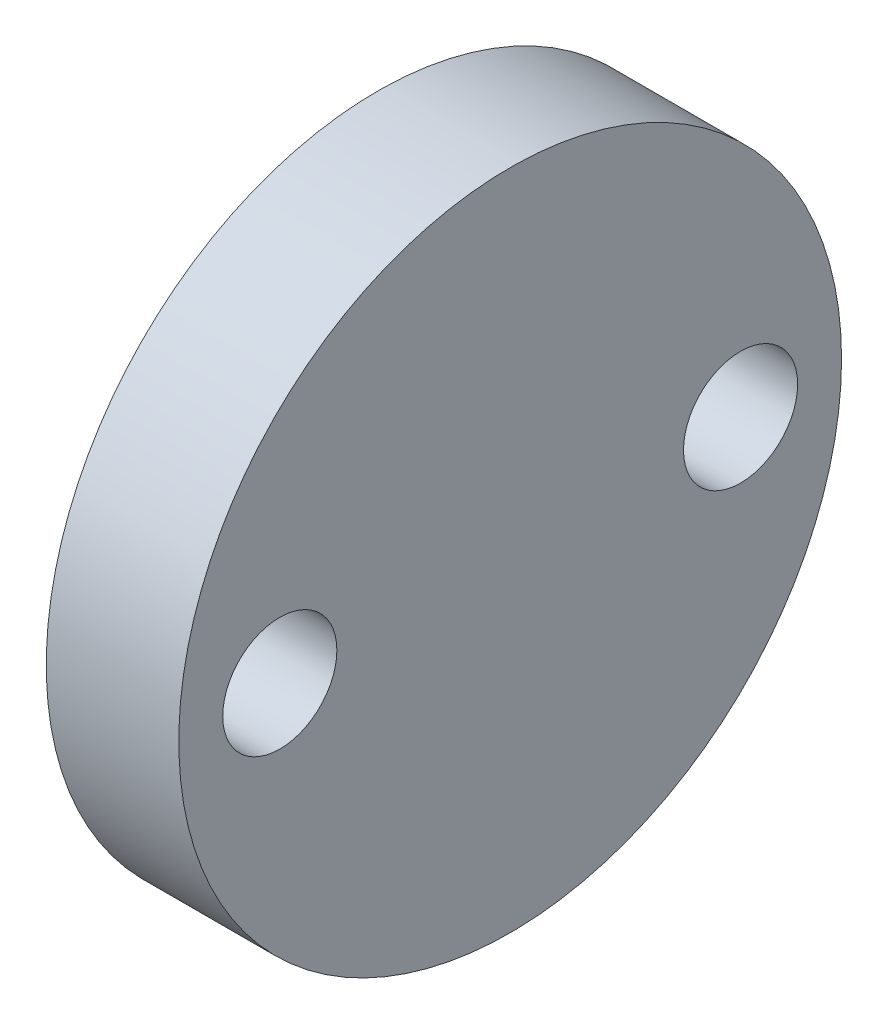
SolidWorks part; units mm, degrees
ref_plane "Front Plane" through (0, 0, 0) normal (0, 0, 1) x (1, 0, 0)
ref_plane "Top Plane" through (0, 0, 0) normal (0, 1, 0) x (1, 0, 0)
ref_plane "Right Plane" through (0, 0, 0) normal (1, 0, 0) x (0, 0, -1)
sketch "Sketch1" plane through (0, 0, 0) normal (1, 0, 0) x (0, 0, -1)
  line L0 (-12.5, 0) -> (12.5, 0) construction
  circle A0 centre (0, 0) radius 12.5
  dimension "D1" = 25
extrude "Boss-Extrude1" add sketch "Sketch1" along normal blind 5
hole_wizard "#18 (0.1695) Diameter Hole2" positions "Sketch5" profile "Sketch6" hole size "#18" standard "ANSI Inch"
sketch "Sketch5" plane through (0, 0, 0) normal (-1, 0, 0) x (0, 0, 1)
  line L0 (-12.5, 0) -> (12.5, 0) construction
  circle A0 centre (0, 0) radius 12.5 construction
  point P0 (-8.69, 0)
  point P2 (8.69, 0)
  dimension "D1" = 3.81
  dimension "D2" = 3.81
sketch "Sketch6" plane through (0, 0, -8.69) normal (0, 1, 0) x (0, 0, 1)
  line L0 (0, 0) -> (0, 11.4026)
  line L1 (0, 11.4026) -> (2.1526, 10.1092)
  line L2 (2.1526, 10.1092) -> (2.1526, 0)
  line L5 (2.1526, 0) -> (0, 0)
  line L10 (0, 11.4026) -> (-2.1526, 10.1092) construction
  line L11 (0, -6.35) -> (0, 107.95) construction
  dimension "Hole Dia." = 4.3053
  dimension "Hole Depth" = 10.1092
  dimension "Drill Angle" = 118
